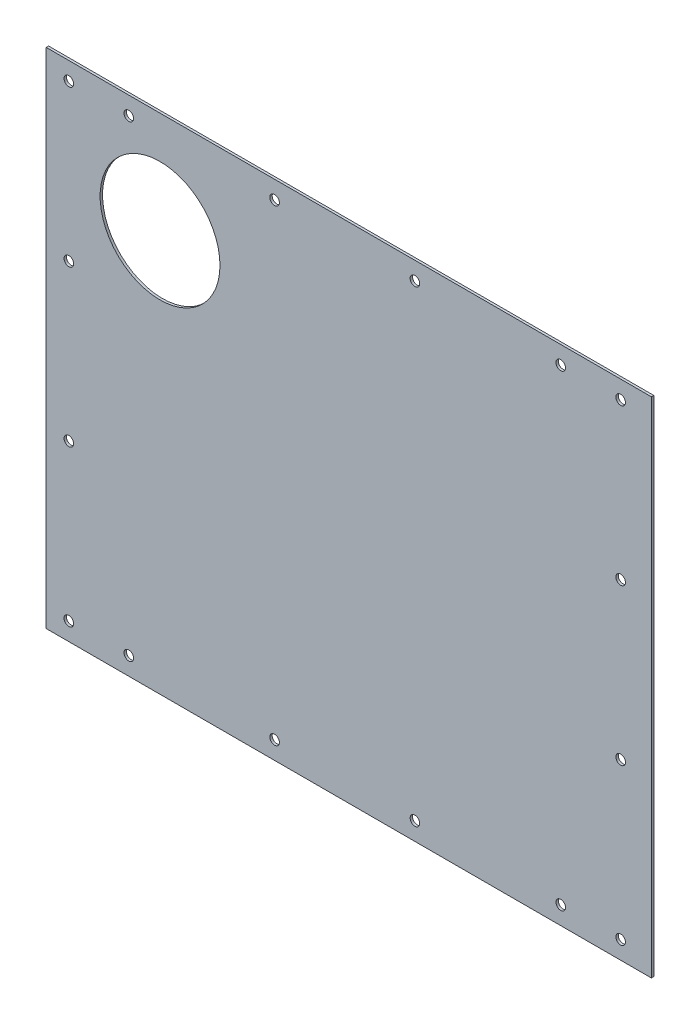
SolidWorks part; units mm, degrees
ref_plane "Plan de face" through (0, 0, 0) normal (0, 0, 1) x (1, 0, 0)
ref_plane "Plan de dessus" through (0, 0, 0) normal (0, 1, 0) x (1, 0, 0)
ref_plane "Plan de droite" through (0, 0, 0) normal (1, 0, 0) x (0, 0, -1)
sketch "Esquisse1" plane through (0, 0, 0) normal (0, 0, 1) x (1, 0, 0)
  line L1 (-252.5, 212.5) -> (252.5, 212.5)
  line L2 (-252.5, 212.5) -> (-252.5, -207.5)
  line L3 (-252.5, -207.5) -> (252.5, -207.5)
  line L4 (252.5, 212.5) -> (252.5, -207.5)
  dimension "D1" = 505
  dimension "D2" = 420
  dimension "D3" = 252.5
  dimension "D4" = 207.5
extrude "Boss.-Extru.1" add sketch "Esquisse1" along normal blind 2
sketch "Esquisse2" plane through (0, 0, 2) normal (0, 0, 1) x (1, 0, 0)
  line L5 (-252.5, 212.5) -> (-252.5, -207.5) construction
  line L6 (252.5, 212.5) -> (-252.5, 212.5) construction
  circle A0 centre (-157.5, 127.5) radius 50
  dimension "D1" = 100
  dimension "D2" = 95
  dimension "D3" = 85
extrude "Enlèv. mat.-Extru.1" cut sketch "Esquisse2" against normal blind 10
sketch "Esquisse3" plane through (0, 0, 2) normal (0, 0, 1) x (1, 0, 0)
  line L0 (-233.6, 197.5) -> (226.84, 197.5) construction
  line L1 (226.84, 197.5) -> (226.84, -192.5) construction
  line L2 (226.84, -192.5) -> (-233.6, -192.5) construction
  line L3 (-233.6, -192.5) -> (-233.6, 197.5) construction
  line L4 (252.5, -207.5) -> (252.5, 212.5) construction
  line L5 (252.5, 212.5) -> (-252.5, 212.5) construction
  line L6 (-252.5, 212.5) -> (-252.5, -207.5) construction
  line L7 (-252.5, -207.5) -> (252.5, -207.5) construction
  line L8 (362.936, -62.5) -> (-345.5336, -62.5) construction
  line L9 (328.912, 67.5) -> (-356.5057, 67.5) construction
  line L10 (55.17, 298.9929) -> (55.17, -246.0427) construction
  line L11 (-61.93, 286.731) -> (-61.93, -245.9554) construction
  line L12 (-183.6, 238.3605) -> (-183.6, -245.9554) construction
  line L13 (176.84, 251.7074) -> (176.84, -240.4576) construction
  circle A0 centre (-233.6, 197.5) radius 4
  circle A1 centre (-183.6, 197.5) radius 4
  circle A2 centre (-61.93, 197.5) radius 4
  circle A3 centre (55.17, 197.5) radius 4
  circle A4 centre (176.84, 197.5) radius 4
  circle A5 centre (226.84, 197.5) radius 4
  circle A6 centre (226.84, 67.5) radius 4
  circle A7 centre (226.84, -62.5) radius 4
  circle A8 centre (226.84, -192.5) radius 4
  circle A9 centre (176.84, -192.5) radius 4
  circle A10 centre (55.17, -192.5) radius 4
  circle A11 centre (-61.93, -192.5) radius 4
  circle A12 centre (-183.6, -192.5) radius 4
  circle A13 centre (-233.6, -192.5) radius 4
  circle A14 centre (-233.6, -62.5) radius 4
  circle A15 centre (-233.6, 67.5) radius 4
  dimension "D11" = 8
  dimension "D15" = 8
  dimension "D16" = 8
  dimension "D17" = 8
  dimension "D18" = 8
  dimension "D19" = 8
  dimension "D20" = 8
  dimension "D21" = 8
  dimension "D22" = 8
  dimension "D23" = 8
  dimension "D24" = 8
  dimension "D25" = 8
  dimension "D26" = 8
  dimension "D27" = 8
  dimension "D28" = 8
  dimension "D29" = 8
  dimension "D1" = 25.66
  dimension "D2" = 15
  dimension "D3" = 18.9
  dimension "D4" = 15
  dimension "D5" = 390
  dimension "D6" = 460.44
  dimension "D7" = 130
  dimension "D8" = 130
  dimension "D9" = 121.67
  dimension "D10" = 121.67
  dimension "D12" = 50
  dimension "D13" = 50
  dimension "D14" = 360.44
extrude "Enlèv. mat.-Extru.2" cut sketch "Esquisse3" against normal blind 10
